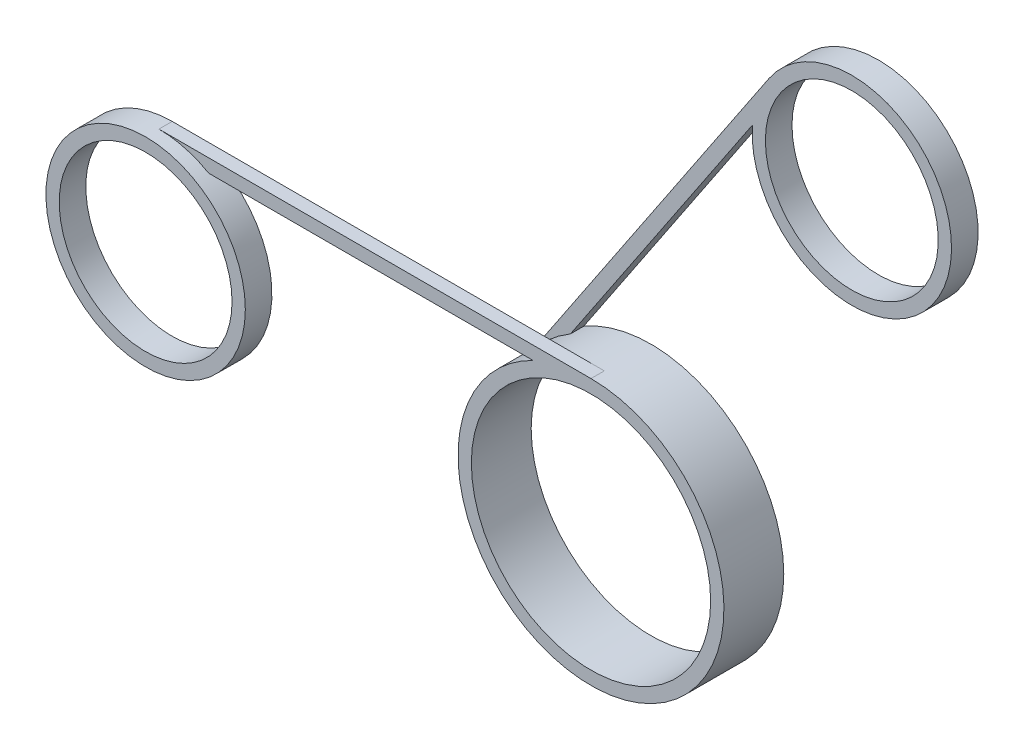
SolidWorks part; units mm, degrees
material "Acciaio in lega fuso"
ref_plane "Piano frontale" through (0, 0, 0) normal (0, 0, 1) x (1, 0, 0)
ref_plane "Piano superiore" through (0, 0, 0) normal (0, 1, 0) x (1, 0, 0)
ref_plane "Piano destro" through (0, 0, 0) normal (1, 0, 0) x (0, 0, -1)
sketch "Sketch1" plane through (0, 0, 0) normal (0, 0, 1) x (1, 0, 0)
  circle A0 centre (0, 0) radius 10
  dimension "D2" = 20
extrude "Boss-Extrude1" add sketch "Sketch1" along normal blind 4.5
sketch "Sketch2" plane through (0, 0, 4.5) normal (0, 0, 1) x (1, 0, 0)
  circle A0 centre (0, 0) radius 9
extrude "Cut-Extrude1" cut sketch "Sketch2" against normal blind 4.5
sketch "Sketch3" plane through (0, 0, 4.5) normal (0, 0, 1) x (1, 0, 0)
  line L0 (0, 0) -> (0, 14.6077) construction
  line L1 (0, 0) -> (-18.978, 0) construction
  line L2 (0, 10) -> (-32.5, 10)
  line L3 (0, 9) -> (-32.5, 9)
  line L4 (-32.5, 9) -> (-32.5, 10)
  line L5 (-32.5, 9) -> (-32.5, -3.1529) construction
  line L6 (0, 10) -> (0, 9)
  circle A0 centre (0, 0) radius 10 construction
  circle A1 centre (0, 0) radius 9 construction
  dimension "D1" = 32.5
extrude "Boss-Extrude2" add sketch "Sketch3" against normal blind 1
sketch "Sketch5" plane through (0, 0, 4.5) normal (0, 0, 1) x (1, 0, 0)
  line L0 (-32.5, 10) -> (-32.5, -3.0917) construction
  circle A0 centre (-32.5, 2.5) radius 7.5
extrude "Boss-Extrude3" add sketch "Sketch5" along normal mid plane 2
sketch "Sketch6" plane through (0, 0, 5.5) normal (0, 0, 1) x (1, 0, 0)
  circle A0 centre (-32.5, 2.5) radius 6.5
  circle A1 centre (-32.5, 2.5) radius 7.5 construction
  dimension "D1" = 1
extrude "Cut-Extrude2" cut sketch "Sketch6" against normal blind 2
sketch "Sketch8" plane through (0, 0, 0) normal (0, 0, -1) x (-1, 0, 0)
  line L0 (0, 0) -> (0, 33.0899) construction
  line L1 (0, 10) -> (37.922, 35.3866) construction
  line L3 (0, 10) -> (32.5, 10) construction
  line L4 (8.1941, 5.7321) -> (-9.8855, 32.7391)
  line L5 (-9.8855, 32.7391) -> (-10.7165, 32.1828)
  line L6 (-10.7165, 32.1828) -> (7.3629, 5.1757)
  line L7 (7.3629, 5.1757) -> (8.1941, 5.7321)
  arc A1 (4.3589, 9) -> (0, 10) centre (0, 0) ccw construction
  circle A2 centre (0, 0) radius 10 construction
  circle A3 centre (0, 0) radius 9 construction
  dimension "D1" = 33.8
  dimension "D2" = 90
  dimension "D3" = 32.5
  dimension "D4" = 90
  dimension "D5" = 1
extrude "Boss-Extrude4" add sketch "Sketch8" against normal blind 1
sketch "Sketch9" plane through (0, 0, 0) normal (0, 0, -1) x (-1, 0, 0)
  line L0 (-9.8855, 32.7391) -> (-28.3955, 20.3477) construction
  line L1 (8.1941, 5.7321) -> (-9.8855, 32.7391) construction
  circle A0 centre (-16.1179, 28.5669) radius 7.5
  dimension "D1" = 90
extrude "Boss-Extrude5" add sketch "Sketch9" along normal mid plane 2
sketch "Sketch10" plane through (0, 0, -1) normal (0, 0, -1) x (-1, 0, 0)
  circle A0 centre (-16.1179, 28.5669) radius 6.5
  circle A1 centre (-16.1179, 28.5669) radius 7.5 construction
  dimension "D1" = 1
extrude "Cut-Extrude3" cut sketch "Sketch10" against normal blind 2
